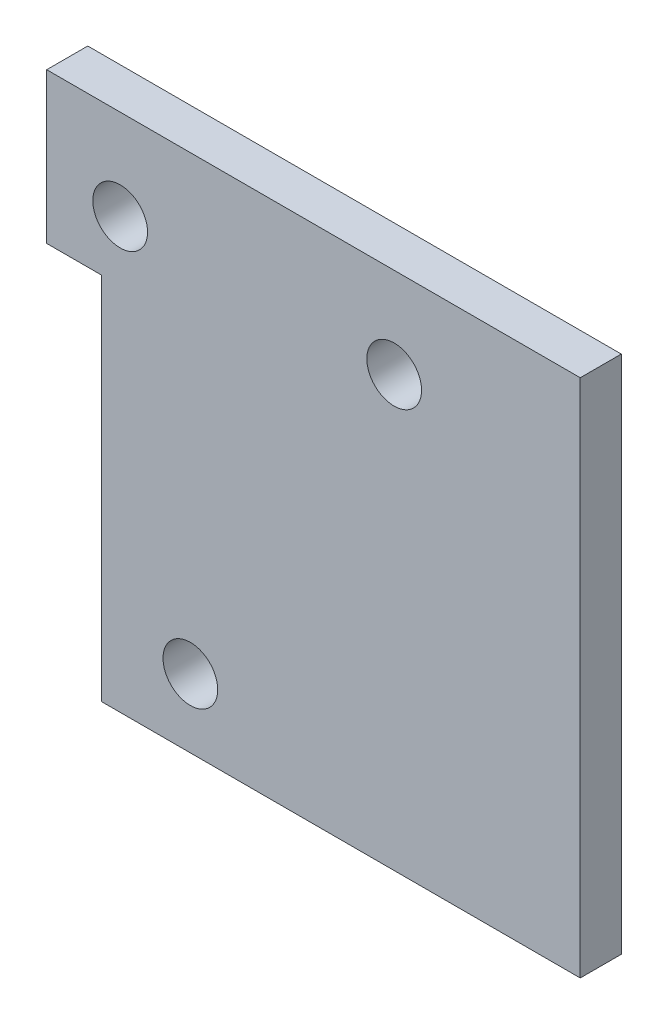
SolidWorks part; units mm, degrees
ref_plane "Front Plane" through (0, 0, 0) normal (0, 0, 1) x (1, 0, 0)
ref_plane "Top Plane" through (0, 0, 0) normal (0, 1, 0) x (1, 0, 0)
ref_plane "Right Plane" through (0, 0, 0) normal (1, 0, 0) x (0, 0, -1)
sketch "Sketch1" plane through (0, 0, 0) normal (0, 0, 1) x (1, 0, 0)
  line L1 (4, 0) -> (39, 0)
  line L2 (0, 27) -> (0, 38)
  line L3 (0, 38) -> (39, 38)
  line L4 (39, 0) -> (39, 38)
  line L7 (0, 27) -> (4, 27)
  line L8 (4, 0) -> (4, 27)
  dimension "D2" = 39
  dimension "D3" = 27
  dimension "D4" = 4
extrude "Boss-Extrude1" add sketch "Sketch1" along normal blind 3
sketch "Sketch2" plane through (0, 0, 3) normal (0, 0, 1) x (1, 0, 0)
  line L0 (0, 38) -> (0, 27) construction
  line L2 (39, 38) -> (0, 38) construction
  line L3 (4, 27) -> (4, 0) construction
  line L4 (4, 0) -> (39, 0) construction
  circle A0 centre (5.37, 31.4) radius 2
  circle A1 centre (25.4, 31.4) radius 2
  circle A2 centre (10.5, 5) radius 2
  dimension "D1" = 4
  dimension "D2" = 4
  dimension "D3" = 4
  dimension "D4" = 5.37
  dimension "D5" = 6.6
  dimension "D6" = 0
  dimension "D7" = 20.03
  dimension "D8" = 6.5
  dimension "D9" = 5
extrude "Cut-Extrude1" cut sketch "Sketch2" against normal blind 3
sketch "Sketch3" plane through (0, 0, 3) normal (0, 0, 1) x (1, 0, 0)
  circle A0 centre (5.37, 31.4) radius 2.5
  circle A1 centre (25.4, 31.4) radius 2.5
  circle A2 centre (10.5, 5) radius 2.5
  circle A3 centre (10.5, 5) radius 2 construction
  circle A4 centre (25.4, 31.4) radius 2 construction
  circle A5 centre (5.37, 31.4) radius 2 construction
  circle A6 centre (10.5, 5) radius 2
  circle A7 centre (25.4, 31.4) radius 2
  circle A8 centre (5.37, 31.4) radius 2
  dimension "D1" = 5
  dimension "D2" = 5
  dimension "D3" = 5
extrude "Boss-Extrude2" add sketch "Sketch3" against normal blind 6
equation "\"D2@Sketch3\"=\"D1@Sketch3\""
equation "\"D3@Sketch3\"=\"D1@Sketch3\""
